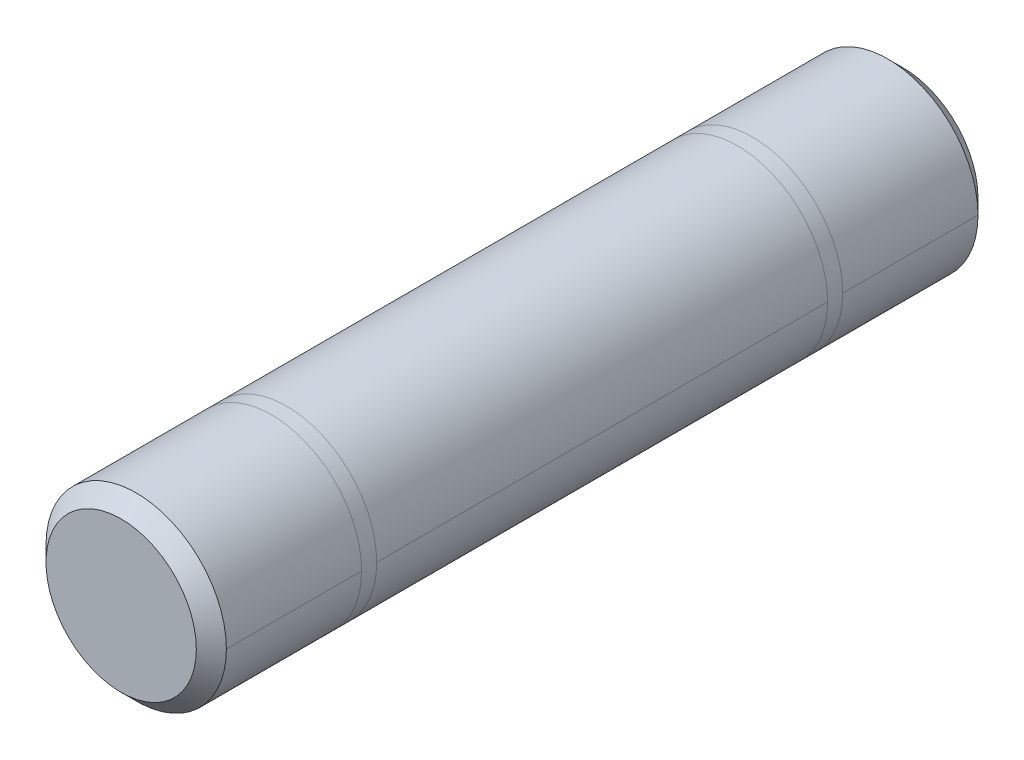
SolidWorks part; units mm, degrees
ref_plane "Plan de face" through (0, 0, 0) normal (0, 0, 1) x (1, 0, 0)
ref_plane "Plan de dessus" through (0, 0, 0) normal (0, 1, 0) x (1, 0, 0)
ref_plane "Plan de droite" through (0, 0, 0) normal (1, 0, 0) x (0, 0, -1)
sketch "Esquisse1" plane through (0, 0, 0) normal (0, 0, 1) x (1, 0, 0)
  circle A0 centre (0, 0) radius 3
  dimension "D1" = 6
extrude "Boss.-Extru.1" add sketch "Esquisse1" along normal blind 26
chamfer "Chanfrein1" distance 0.5 angle 45 2 edges at (3, 0, 0) (3, 0, 26)
sketch "Esquisse2" plane through (0, 0, 0) normal (1, 0, 0) x (0, 0, -1)
  line L0 (-26, 2.5) -> (-26, -2.5) construction
  line L1 (-26, 3.01) -> (-21, 3.01)
  line L2 (-26, 3.01) -> (-26, 3)
  line L3 (-26, 3) -> (-21, 3)
  line L4 (-21, 3.01) -> (-21, 3)
  line L5 (-26, 3.01) -> (-21, 3) construction
  line L6 (-26, 3) -> (-21, 3.01) construction
  line L7 (-20.5, 3.01) -> (-5.5, 3.01)
  line L9 (-20.5, 3) -> (-5.5, 3)
  line L11 (-20.5, 3.01) -> (-5.5, 3) construction
  line L12 (-20.5, 3) -> (-5.5, 3.01) construction
  line L13 (-5, 3.01) -> (0, 3.01)
  line L14 (-5, 3.01) -> (-5, 3)
  line L15 (-5, 3) -> (0, 3)
  line L16 (0, 3.01) -> (0, 3)
  line L17 (-5, 3.01) -> (0, 3) construction
  line L18 (-5, 3) -> (0, 3.01) construction
  line L19 (0, -2.5) -> (0, 2.5) construction
  line L20 (-20.5, 3.01) -> (-20.5, 3)
  line L21 (-5.5, 3) -> (-5.5, 3.01)
  line L22 (-0.5, 3) -> (-25.5, 3) construction
  line L23 (0, 0) -> (-31.7265, 0) construction
  point P0 (-23.5, 3.005)
  point P5 (-13, 3.005)
  point P10 (-2.5, 3.005)
  dimension "D1" = 15
  dimension "26/2" = 13
  dimension "D2" = 0
  dimension "D3" = 0.01
  dimension "D4" = 0.01
  dimension "D5" = 0.01
  dimension "D6" = 0
ref_plane "Plan1" through (0, 0, 5) normal (0, 0, 1) x (1, 0, 0)
ref_plane "Plan2" through (0, 0, 5.5) normal (0, 0, 1) x (1, 0, 0)
ref_plane "Plan3" through (0, 0, 20.5) normal (0, 0, 1) x (1, 0, 0)
ref_plane "Plan4" through (0, 0, 21) normal (0, 0, 1) x (1, 0, 0)
ref_plane "Plan5" through (0, 0, 26) normal (0, 0, 1) x (1, 0, 0)
sketch "Esquisse3" plane through (0, 0, 5) normal (0, 0, 1) x (1, 0, 0)
  circle A0 centre (0, 0) radius 3
sketch "Esquisse4" plane through (0, 0, 5.5) normal (0, 0, 1) x (1, 0, 0)
  circle A0 centre (0, 0) radius 3
sketch "Esquisse5" plane through (0, 0, 20.5) normal (0, 0, 1) x (1, 0, 0)
  circle A0 centre (0, 0) radius 3
sketch "Esquisse6" plane through (0, 0, 21) normal (0, 0, 1) x (1, 0, 0)
  circle A0 centre (0, 0) radius 3
  circle A1 centre (0, 0) radius 3 construction
  circle A2 centre (0, 0) radius 3
sketch "Esquisse7" plane through (0, 0, 26) normal (0, 0, 1) x (1, 0, 0)
  circle A0 centre (0, 0) radius 3
split line "Ligne de séparation11"
split line "Ligne de séparation12"
split line "Ligne de séparation13"
split line "Ligne de séparation14"
ref_plane "Plan6" through (0, 0, 0) normal (0, 1, 0) x (1, 0, 0)
split line "Ligne de séparation15"
split line "Ligne de séparation16"
split line "Ligne de séparation17"
